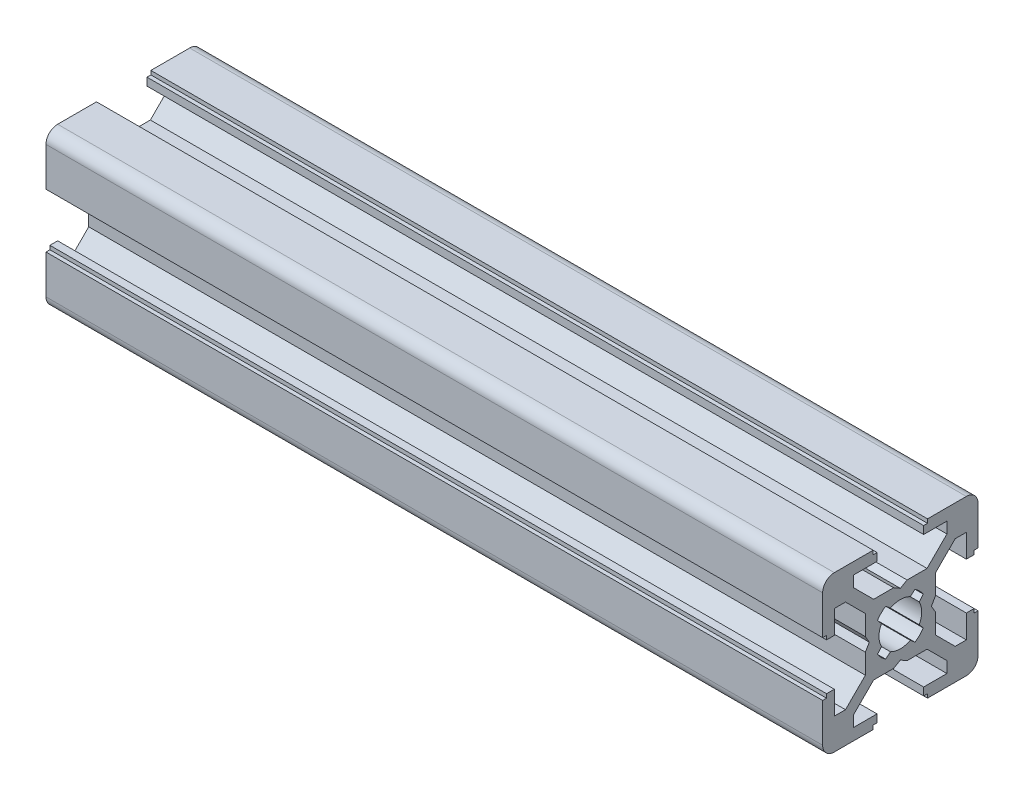
SolidWorks part; units mm, degrees
ref_plane "Front Plane" through (0, 0, 0) normal (0, 0, 1) x (1, 0, 0)
ref_plane "Top Plane" through (0, 0, 0) normal (0, 1, 0) x (1, 0, 0)
ref_plane "Right Plane" through (0, 0, 0) normal (1, 0, 0) x (0, 0, -1)
ref_plane "Plane1" through (100, 0, 0) normal (1, 0, 0) x (0, 0, -1)
sketch "Sketch1" plane through (100, 0, 0) normal (1, 0, 0) x (0, 0, -1)
  line L0 (7.0607, -6) -> (4.5, -3.4393)
  line L1 (4.5, -3.4393) -> (4.5, -0.866)
  line L2 (4.5, -0.866) -> (4, 0)
  line L3 (4, 0) -> (4.5, 0.866)
  line L4 (4.5, 0.866) -> (4.5, 3.4393)
  line L5 (4.5, 3.4393) -> (7.0607, 6)
  line L6 (7.0607, 6) -> (8.5, 6)
  line L7 (8.5, 6) -> (8.5, 3)
  line L8 (8.5, 3) -> (9.5, 3)
  line L9 (9.5, 3) -> (9.5, 3.5)
  line L10 (9.5, 3.5) -> (10, 3.5)
  line L11 (10, 3.5) -> (10, 8.5)
  line L12 (8.5, 10) -> (3.5, 10)
  line L13 (3.5, 10) -> (3.5, 9.5)
  line L14 (3.5, 9.5) -> (3, 9.5)
  line L15 (3, 9.5) -> (3, 8.5)
  line L16 (3, 8.5) -> (6, 8.5)
  line L17 (6, 8.5) -> (6, 7.0607)
  line L18 (6, 7.0607) -> (3.4393, 4.5)
  line L19 (3.4393, 4.5) -> (0.866, 4.5)
  line L20 (0.866, 4.5) -> (0, 4)
  line L21 (0, 4) -> (-0.866, 4.5)
  line L22 (-0.866, 4.5) -> (-3.4393, 4.5)
  line L23 (-3.4393, 4.5) -> (-6, 7.0607)
  line L24 (-6, 7.0607) -> (-6, 8.5)
  line L25 (-6, 8.5) -> (-3, 8.5)
  line L26 (-3, 8.5) -> (-3, 9.5)
  line L27 (-3, 9.5) -> (-3.5, 9.5)
  line L28 (-3.5, 9.5) -> (-3.5, 10)
  line L29 (-3.5, 10) -> (-8.5, 10)
  line L30 (-10, 8.5) -> (-10, 3.5)
  line L31 (-10, 3.5) -> (-9.5, 3.5)
  line L32 (-9.5, 3.5) -> (-9.5, 3)
  line L33 (-9.5, 3) -> (-8.5, 3)
  line L34 (-8.5, 3) -> (-8.5, 6)
  line L35 (-8.5, 6) -> (-7.0607, 6)
  line L36 (-7.0607, 6) -> (-4.5, 3.4393)
  line L37 (-4.5, 3.4393) -> (-4.5, 0.866)
  line L38 (-4.5, 0.866) -> (-4, 0)
  line L39 (-4, 0) -> (-4.5, -0.866)
  line L40 (-4.5, -0.866) -> (-4.5, -3.4393)
  line L41 (-4.5, -3.4393) -> (-7.0607, -6)
  line L42 (-7.0607, -6) -> (-8.5, -6)
  line L43 (-8.5, -6) -> (-8.5, -3)
  line L44 (-8.5, -3) -> (-9.5, -3)
  line L45 (-9.5, -3) -> (-9.5, -3.5)
  line L46 (-9.5, -3.5) -> (-10, -3.5)
  line L47 (-10, -3.5) -> (-10, -8.5)
  line L48 (-8.5, -10) -> (-3.5, -10)
  line L49 (-3.5, -10) -> (-3.5, -9.5)
  line L50 (-3.5, -9.5) -> (-3, -9.5)
  line L51 (-3, -9.5) -> (-3, -8.5)
  line L52 (-3, -8.5) -> (-6, -8.5)
  line L53 (-6, -8.5) -> (-6, -7.0607)
  line L54 (-6, -7.0607) -> (-3.4393, -4.5)
  line L55 (-3.4393, -4.5) -> (-0.866, -4.5)
  line L56 (-0.866, -4.5) -> (0, -4)
  line L57 (0, -4) -> (0.866, -4.5)
  line L58 (0.866, -4.5) -> (3.4393, -4.5)
  line L59 (3.4393, -4.5) -> (6, -7.0607)
  line L60 (6, -7.0607) -> (6, -8.5)
  line L61 (6, -8.5) -> (3, -8.5)
  line L62 (3, -8.5) -> (3, -9.5)
  line L63 (3, -9.5) -> (3.5, -9.5)
  line L64 (3.5, -9.5) -> (3.5, -10)
  line L65 (3.5, -10) -> (8.5, -10)
  line L66 (10, -8.5) -> (10, -3.5)
  line L67 (10, -3.5) -> (9.5, -3.5)
  line L68 (9.5, -3.5) -> (9.5, -3)
  line L69 (9.5, -3) -> (8.5, -3)
  line L70 (8.5, -3) -> (8.5, -6)
  line L71 (8.5, -6) -> (7.0607, -6)
  line L72 (2.9478, 1.887) -> (2.4357, 1.2767)
  line L73 (2.4357, -1.2767) -> (2.9478, -1.887)
  line L74 (1.8871, -2.9477) -> (1.2769, -2.4356)
  line L75 (-1.2769, -2.4356) -> (-1.8871, -2.9477)
  line L76 (-2.9478, -1.887) -> (-2.4357, -1.2767)
  line L77 (-2.4357, 1.2767) -> (-2.9478, 1.887)
  line L78 (-1.8871, 2.9477) -> (-1.2769, 2.4356)
  line L79 (1.2769, 2.4356) -> (1.8871, 2.9477)
  arc A0 (10, 8.5) -> (8.5, 10) centre (8.5, 8.5) ccw
  arc A1 (-8.5, 10) -> (-10, 8.5) centre (-8.5, 8.5) ccw
  arc A2 (-10, -8.5) -> (-8.5, -10) centre (-8.5, -8.5) ccw
  arc A3 (8.5, -10) -> (10, -8.5) centre (8.5, -8.5) ccw
  arc A4 (1.8871, 2.9477) -> (2.9478, 1.887) centre (0, 0) cw
  arc A5 (2.4357, 1.2767) -> (2.4357, -1.2767) centre (0, 0) cw
  arc A6 (2.9478, -1.887) -> (1.8871, -2.9477) centre (0, 0) cw
  arc A7 (1.2769, -2.4356) -> (-1.2769, -2.4356) centre (0, 0) cw
  arc A8 (-1.8871, -2.9477) -> (-2.9478, -1.887) centre (0, 0) cw
  arc A9 (-2.4357, -1.2767) -> (-2.4357, 1.2767) centre (0, 0) cw
  arc A10 (-2.9478, 1.887) -> (-1.8871, 2.9477) centre (0, 0) cw
  arc A11 (-1.2769, 2.4356) -> (1.2769, 2.4356) centre (0, 0) cw
extrude "Boss-Extrude1" add sketch "Sketch1" against normal blind 100
